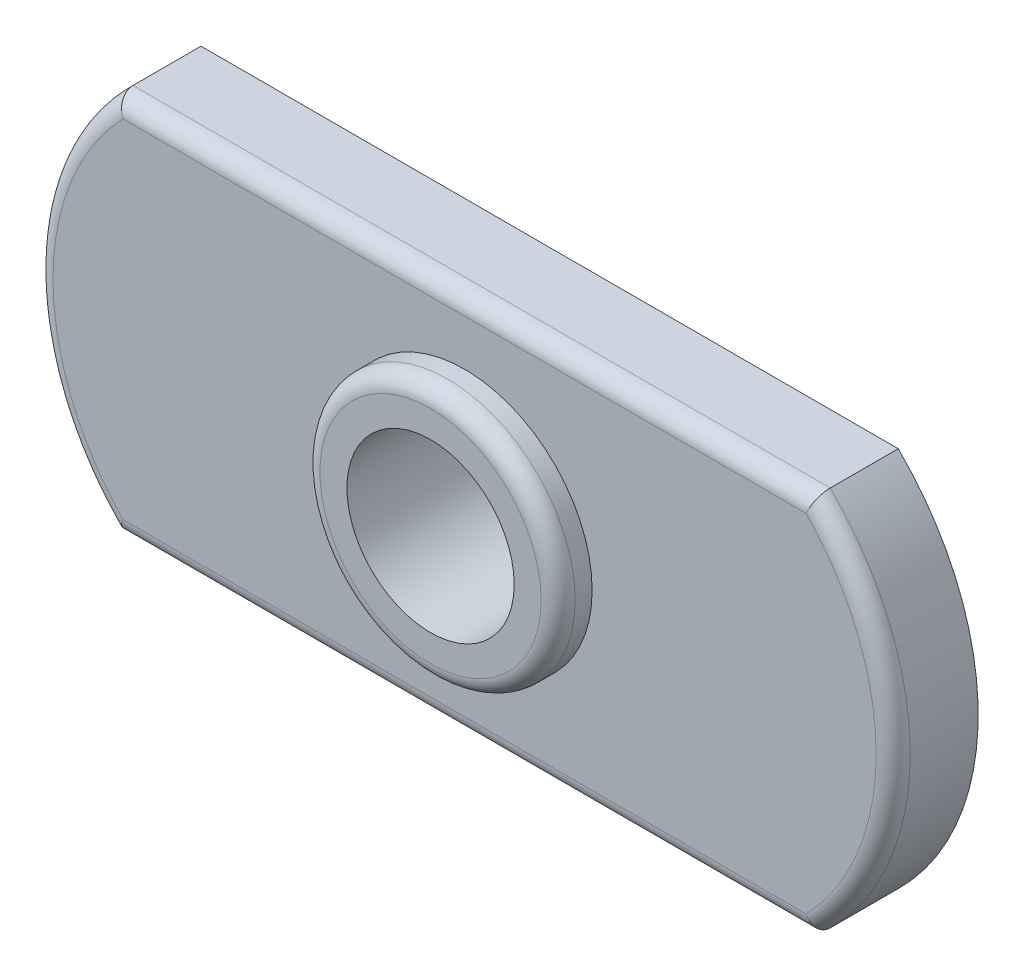
SolidWorks part; units mm, degrees
material "Chrome Stainless Steel"
ref_plane "Front Plane" through (0, 0, 0) normal (0, 0, 1) x (1, 0, 0)
ref_plane "Top Plane" through (0, 0, 0) normal (0, 1, 0) x (1, 0, 0)
ref_plane "Right Plane" through (0, 0, 0) normal (1, 0, 0) x (0, 0, -1)
ref_plane "Plane1"
sketch "Sketch1" plane through (0, 0, 0) normal (0, 0, 1) x (1, 0, 0)
  line L0 (-10.25, -5.6) -> (10.25, -5.6)
  line L1 (10.25, 5.6) -> (-10.25, 5.6)
  arc A0 (-10.25, 5.6) -> (-10.25, -5.6) centre (-4.7527, 0) ccw
  arc A1 (10.25, -5.6) -> (10.25, 5.6) centre (4.7527, 0) ccw
  dimension "D1" = 11.2
  dimension "D2" = 20.5
extrude "Extrusion1" add sketch "Sketch1" along normal blind 2.5
sketch "Sketch2" plane through (0, 0, 2.5) normal (0, 0, 1) x (1, 0, 0)
  circle A0 centre (0, 0) radius 3.75
  dimension "D1" = 7.5
extrude "Extrusion2" add sketch "Sketch2" along normal blind 1
hole_wizard "Hole1" positions "Sketch4" profile "Sketch3" legacy end condition through all
sketch "Sketch4" plane through (0, 0, 3.5) normal (0, 0, 1) x (1, 0, 0)
  point P1 (0, 0)
sketch "Sketch3" plane through (0, 0, 3.5) normal (1, 0, 0) x (0, -1, 0)
  line L0 (0, 0) -> (0, 3.5)
  line L1 (0, 3.5) -> (2.4585, 3.5)
  line L2 (2.4585, 3.5) -> (2.4585, 0)
  line L3 (2.4585, 0) -> (0, 0)
  line L4 (0, 110) -> (0, -10) construction
  dimension "Diameter" = 4.917
  dimension "Depth" = 3.5
cosmetic thread "Cosmetic Thread1" parameters "D1"=3.5, "D2"=6.294
fillet "Fillet1" radius 0.5 5 edges at (-12.6, 0, 2.5) (0, 5.6, 2.5) (12.6, 0, 2.5) (0, -5.6, 2.5) (3.75, 0, 3.5)
